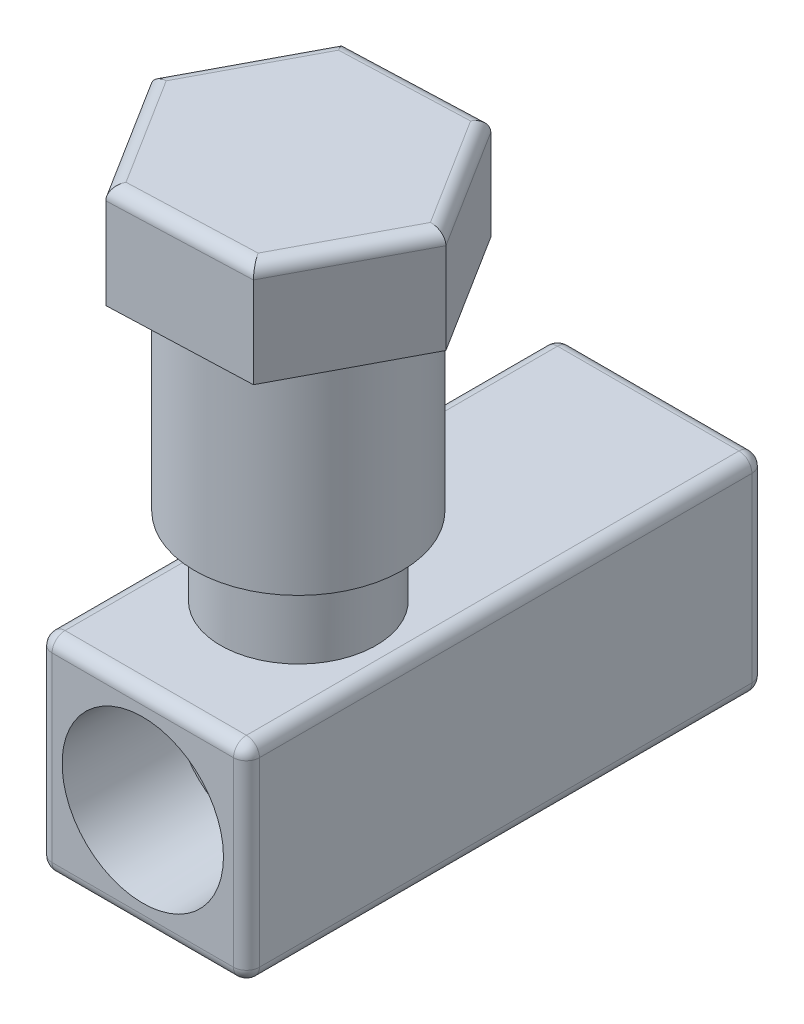
SolidWorks part; units mm, degrees
ref_plane "Front Plane" through (0, 0, 0) normal (0, 0, 1) x (1, 0, 0)
ref_plane "Top Plane" through (0, 0, 0) normal (0, 1, 0) x (1, 0, 0)
ref_plane "Right Plane" through (0, 0, 0) normal (1, 0, 0) x (0, 0, -1)
sketch "Sketch1" plane through (0, 0, 0) normal (0, 0, 1) x (1, 0, 0)
  line L1 (0, 0) -> (25.4, 0)
  line L2 (0, 0) -> (0, 25.4)
  line L3 (0, 25.4) -> (25.4, 25.4)
  line L4 (25.4, 0) -> (25.4, 25.4)
  dimension "D1" = 25.4
  dimension "D2" = 25.4
extrude "Boss-Extrude1" add sketch "Sketch1" along normal blind 63.5
hole_wizard "1/2 NPT Tapped Hole1" positions "Sketch3" profile "Sketch2" size "1/2" standard "Ansi Inch"
sketch "Sketch3" plane through (0, 0, 63.5) normal (0, 0, 1) x (1, 0, 0)
  line L3 (0, 12.7) -> (25.4, 12.7) construction
  line L4 (0, 25.4) -> (0, 0) construction
  line L5 (25.4, 0) -> (25.4, 25.4) construction
  point P0 (12.7, 12.7)
sketch "Sketch2" plane through (12.7, 12.7, 63.5) normal (1, 0, 0) x (0, -1, 0)
  line L0 (0, 0) -> (0, 27.9705)
  line L1 (8.9281, 22.606) -> (0, 27.9705)
  line L2 (-8.9281, 22.606) -> (0, 27.9705) construction
  line L3 (8.9281, 22.606) -> (8.9281, 13.462)
  line L4 (8.9281, 13.462) -> (9.4797, 13.462)
  line L5 (9.4797, 13.462) -> (9.8828, 0)
  line L6 (-9.4797, 13.462) -> (-9.8828, 0) construction
  line L7 (9.8828, 0) -> (0, 0)
  line L8 (0, -6.35) -> (0, 107.95) construction
  line L11 (-8.9281, 13.462) -> (-9.4797, 13.462) construction
  dimension "Tap Drill Dia." = 17.8562
  dimension "Tap Drill Depth" = 22.606
  dimension "Thread Dia." = 19.7656
  dimension "Thread Angle" = 3.43
  dimension "Thread Depth" = 13.462
  dimension "Drill Angle" = 118
cosmetic thread "Hole Thread2" parameters "D1"=13.462
sketch "Sketch4" plane through (0, 25.4, 0) normal (0, 1, 0) x (1, 0, 0)
  line L0 (12.7, -63.5) -> (12.7, 0) construction
  line L1 (25.4, -63.5) -> (0, -63.5) construction
  line L2 (25.4, 0) -> (0, 0) construction
  circle A0 centre (12.7, -44.45) radius 9.525
  dimension "D2" = 19.05
  dimension "D1" = 19.05
extrude "Boss-Extrude2" add sketch "Sketch4" along normal blind 9.525
sketch "Sketch5" plane through (0, 34.925, 0) normal (0, 1, 0) x (1, 0, 0)
  circle A0 centre (12.7, -44.45) radius 12.7
  circle A1 centre (12.7, -44.45) radius 9.525
  circle A2 centre (12.7, -44.45) radius 9.525 construction
  dimension "D1" = 0
  dimension "D2" = 3.175
extrude "Boss-Extrude3" add sketch "Sketch5" along normal blind 25.4
sketch "Sketch6" plane through (0, 60.325, 0) normal (0, 1, 0) x (1, 0, 0)
  line L1 (3.4223, -29.6743) -> (-4.735, -45.0968)
  line L2 (-4.735, -45.0968) -> (4.5427, -59.8726)
  line L3 (4.5427, -59.8726) -> (21.9777, -59.2257)
  line L4 (21.9777, -59.2257) -> (30.135, -43.8032)
  line L5 (30.135, -43.8032) -> (20.8573, -29.0274)
  line L6 (20.8573, -29.0274) -> (3.4223, -29.6743)
  circle A0 centre (12.7, -44.45) radius 15.1095 construction
extrude "Boss-Extrude4" add sketch "Sketch6" along normal blind 12.7
hole_wizard "1/2 NPT Tapped Hole2" positions "Sketch8" profile "Sketch7" size "1/2" standard "Ansi Inch"
sketch "Sketch8" plane through (0, 0, 0) normal (0, 0, -1) x (-1, 0, 0)
  line L0 (-12.7, 25.4) -> (-12.7, 0) construction
  line L1 (-25.4, 25.4) -> (0, 25.4) construction
  line L2 (0, 0) -> (-25.4, 0) construction
  point P0 (-12.7, 12.7)
cosmetic thread "Hole Thread3" parameters "D1"=13.462
sketch "Sketch7" plane through (12.7, 12.7, 0) normal (1, 0, 0) x (0, 1, 0)
  line L0 (0, 0) -> (0, 27.9705)
  line L1 (8.9281, 22.606) -> (0, 27.9705)
  line L2 (-8.9281, 22.606) -> (0, 27.9705) construction
  line L3 (8.9281, 22.606) -> (8.9281, 13.462)
  line L4 (8.9281, 13.462) -> (9.4797, 13.462)
  line L5 (9.4797, 13.462) -> (9.8828, 0)
  line L6 (-9.4797, 13.462) -> (-9.8828, 0) construction
  line L7 (9.8828, 0) -> (0, 0)
  line L8 (0, -6.35) -> (0, 107.95) construction
  line L11 (-8.9281, 13.462) -> (-9.4797, 13.462) construction
  dimension "Tap Drill Dia." = 17.8562
  dimension "Tap Drill Depth" = 22.606
  dimension "Thread Dia." = 19.7656
  dimension "Thread Angle" = 3.43
  dimension "Thread Depth" = 13.462
  dimension "Drill Angle" = 118
fillet "Fillet1" radius 1.5875 18 edges at (25.4, 12.7, 63.5) (25.4, 25.4, 31.75) (25.4, 12.7, 0) (0, 25.4, 31.75) (0, 12.7, 63.5) (0, 12.7, 0) (0, 0, 31.75) (12.7, 0, 63.5) (25.4, 0, 31.75) (12.7, 0, 0) (25.4962, 73.025, 36.4153) (26.0563, 73.025, 51.5145) (13.2602, 73.025, 59.5492) (-0.0962, 73.025, 52.4847) (-0.6563, 73.025, 37.3855) (12.1398, 73.025, 29.3508) (12.7, 25.4, 63.5) (12.7, 25.4, 0)
